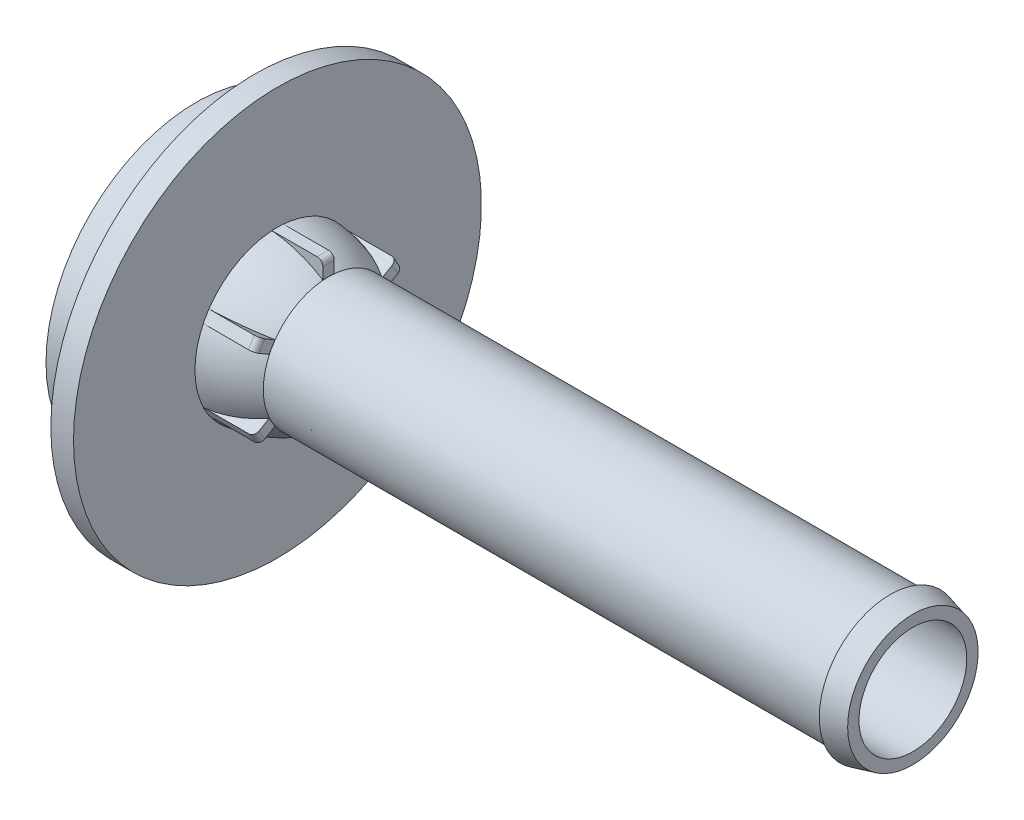
SolidWorks part; units mm, degrees
material "PE Low/Medium Density"
ref_plane "Front Plane" through (0, 0, 0) normal (0, 0, 1) x (1, 0, 0)
ref_plane "Top Plane" through (0, 0, 0) normal (0, 1, 0) x (1, 0, 0)
ref_plane "Right Plane" through (0, 0, 0) normal (1, 0, 0) x (0, 0, -1)
sketch "Sketch1" plane through (0, 0, 0) normal (1, 0, 0) x (0, 0, -1)
  circle A0 centre (0, 0) radius 2.921
  dimension "D1" = 5.842
extrude "Boss-Extrude1" add sketch "Sketch1" along normal blind 26.162
sketch "Sketch3" plane through (0, 0, 0) normal (0, 0, 1) x (1, 0, 0)
  line L0 (0, 0) -> (5.3594, 0) construction
  line L2 (0, 2.921) -> (0, 2.3048)
  line L5 (-2.286, 3.6953) -> (-2.286, 3.1852)
  arc A0 (0, 2.921) -> (-2.286, 3.6953) centre (-2.7261, -1.3656) ccw
  arc A1 (0, 2.3048) -> (-2.286, 3.1852) centre (-2.7261, -1.3656) ccw
  arc A2 (-0.2726, 2.4923) -> (-2.33, 3.1893) centre (-2.7261, -1.3656) ccw construction
  dimension "D3" = 0.508
  dimension "D1" = 5.08
  dimension "D2" = 2.286
revolve "Revolve2" add sketch "Sketch3" angle 360 about L0
sketch "Sketch4" plane through (-2.286, 0, 0) normal (-1, 0, 0) x (0, 0, 1)
  circle A0 centre (0, 0) radius 9.1313
  dimension "D1" = 18.2626
extrude "Boss-Extrude3" add sketch "Sketch4" along normal blind 1.016
sketch "Sketch6" plane through (-3.302, 0, 0) normal (-1, 0, 0) x (0, 0, 1)
  circle A0 centre (0, 0) radius 6.731
  dimension "D1" = 13.462
extrude "Boss-Extrude4" add sketch "Sketch6" along normal blind 2.6162
sketch "Sketch7" plane through (-5.9182, 0, 0) normal (-1, 0, 0) x (0, 0, 1)
  circle A2 centre (0, 0) radius 6.223
  circle A3 centre (0, 0) radius 6.223
  dimension "D1" = 0.508
extrude "Cut-Extrude1" cut sketch "Sketch7" against normal blind 2.6162
sketch "Sketch8" plane through (-3.302, 0, 0) normal (-1, 0, 0) x (0, 0, 1)
  circle A0 centre (0, 0) radius 4.1275
  dimension "D1" = 8.255
extrude "Boss-Extrude5" add sketch "Sketch8" along normal blind 4.191
sketch "Sketch9" plane through (-7.493, 0, 0) normal (-1, 0, 0) x (0, 0, 1)
  circle A2 centre (0, 0) radius 3.1115
  circle A3 centre (0, 0) radius 3.1115
  dimension "D1" = 1.016
extrude "Cut-Extrude2" cut sketch "Sketch9" against normal blind 5.207
sketch "Sketch10" plane through (26.162, 0, 0) normal (1, 0, 0) x (0, 0, -1)
  circle A2 centre (0, 0) radius 2.413
  circle A3 centre (0, 0) radius 2.413
  dimension "D1" = 0.508
extrude "Cut-Extrude3" cut sketch "Sketch10" against normal through all
sketch "Sketch12" plane through (0, 0, 0) normal (0, 0, 1) x (1, 0, 0)
  line L0 (-2.286, 3.6953) -> (0, 3.6953)
  line L1 (0, 3.6953) -> (0, 2.921)
  arc A0 (0, 2.921) -> (-2.286, 3.6953) centre (-2.7261, -1.3656) ccw construction
  arc A1 (0, 2.921) -> (-2.286, 3.6953) centre (-2.7261, -1.3656) ccw
extrude "Boss-Extrude7" add sketch "Sketch12" along normal mid plane 0.508 separate body
fillet "Fillet1" radius 0.254 1 edges at (0, 3.6953, 0)
pattern_circular "CirPattern5" count 6 over 360 about axis through (0, 0, 0) along (1, 0, 0) of bodies 111
ref_plane "Plane1" through (16.6624, 0, 0) normal (1, 0, 0) x (0, 0, -1)
sketch "Sketch13" plane through (16.6624, 0, 0) normal (1, 0, 0) x (0, 0, -1)
  circle A1 centre (0, 0) radius 2.413 construction
  circle A2 centre (0, 0) radius 1.397
  circle A3 centre (0, 0) radius 1.397
  circle A4 centre (0, 0) radius 2.413
  dimension "D1" = 1.016
extrude "Boss-Extrude8" add sketch "Sketch13" along normal blind 3.429
sketch "Sketch14" plane through (16.6624, 0, 0) normal (1, 0, 0) x (0, 0, -1)
  line L0 (0, 0) -> (1.397, 2.4197) construction
  line L1 (0.254, 2.921) -> (0.254, 3.4413) construction
  line L4 (0.9798, 2.2051) -> (0.4669, 1.3167)
  line L6 (1.4198, 1.9511) -> (0.9068, 1.0627)
  line L8 (1.2495, 2.1642) -> (2.536, 4.3925) construction
  line L9 (0.9798, -2.2051) -> (0.4669, -1.3167)
  line L10 (1.4198, -1.9511) -> (0.9068, -1.0627)
  line L11 (-2.3996, 0.254) -> (-1.3737, 0.254)
  line L12 (-2.3996, -0.254) -> (-1.3737, -0.254)
  circle A0 centre (0, 0) radius 1.397 construction
  arc A1 (0.9068, 1.0627) -> (0.4669, 1.3167) centre (0, 0) ccw
  circle A2 centre (0, 0) radius 2.413 construction
  arc A3 (1.4198, 1.9511) -> (0.9798, 2.2051) centre (0, 0) ccw
  arc A4 (0.4669, -1.3167) -> (0.9068, -1.0627) centre (0, 0) ccw
  arc A5 (0.9798, -2.2051) -> (1.4198, -1.9511) centre (0, 0) ccw
  arc A6 (-1.3737, 0.254) -> (-1.3737, -0.254) centre (0, 0) ccw
  arc A7 (-2.3996, 0.254) -> (-2.3996, -0.254) centre (0, 0) ccw
  point P7 (0.6985, 1.2098)
  point P27 (0, 0)
  dimension "D1" = 30
  dimension "D2" = 0.508
  dimension "D3" = 3
extrude "Cut-Extrude4" cut sketch "Sketch14" along normal blind 3.429
sketch "Sketch15" plane through (0, 0, 0) normal (0, 0, 1) x (1, 0, 0)
  line L0 (26.162, 2.921) -> (25.146, 3.175)
  line L1 (25.146, 3.175) -> (25.146, 2.921)
  line L2 (26.162, 2.921) -> (0, 2.921) construction
  line L3 (25.146, 2.921) -> (26.162, 2.921)
  line L4 (-10.4357, 0) -> (38.1777, 0) construction
  dimension "D1" = 1.016
  dimension "D2" = 6.35
revolve "Revolve3" add sketch "Sketch15" angle 360 about L4
